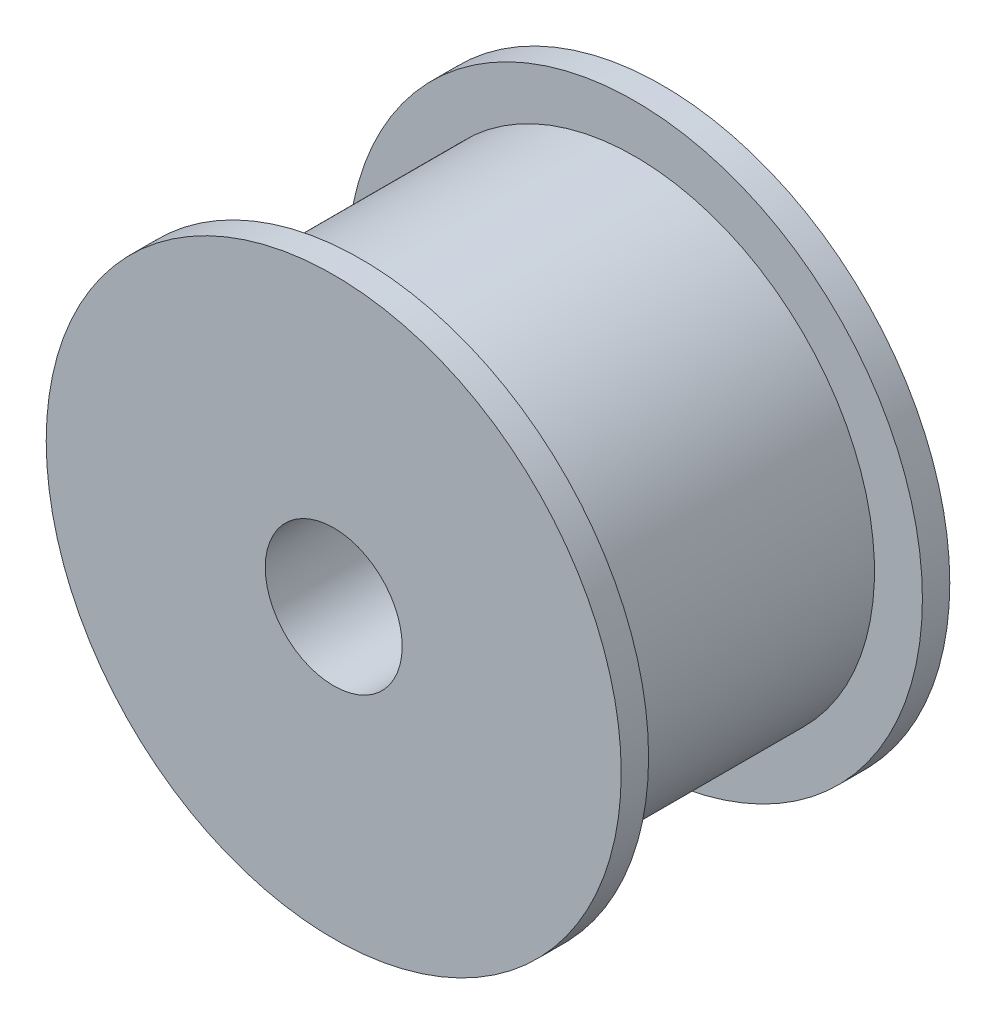
SolidWorks part; units mm, degrees
ref_plane "Plan de face" through (0, 0, 0) normal (0, 0, 1) x (1, 0, 0)
ref_plane "Plan de dessus" through (0, 0, 0) normal (0, 1, 0) x (1, 0, 0)
ref_plane "Plan de droite" through (0, 0, 0) normal (1, 0, 0) x (0, 0, -1)
sketch "Esquisse1" plane through (0, 0, 0) normal (0, 0, 1) x (1, 0, 0)
  circle A0 centre (0, 0) radius 2.5
  circle A1 centre (0, 0) radius 10.5
extrude "Boss.-Extru.1" add sketch "Esquisse1" along normal blind 1 contours A1 A0
sketch "Esquisse2" plane through (0, 0, 0) normal (0, 0, -1) x (-1, 0, 0)
  circle A0 centre (0, 0) radius 2.5
  circle A1 centre (0, 0) radius 8.75
extrude "Boss.-Extru.2" add sketch "Esquisse2" along normal blind 10
sketch "Esquisse3" plane through (0, 0, -10) normal (0, 0, -1) x (-1, 0, 0)
  circle A0 centre (0, 0) radius 2.5
  circle A1 centre (0, 0) radius 10.5
extrude "Boss.-Extru.3" add sketch "Esquisse3" along normal blind 1
